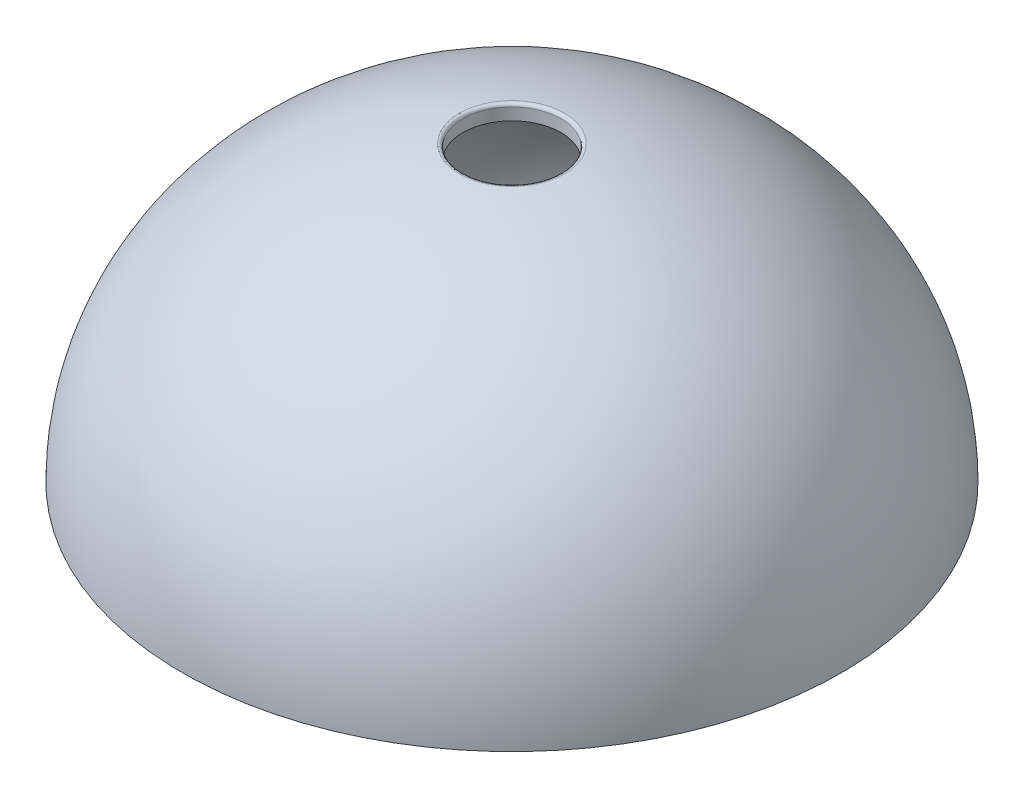
SolidWorks part; units mm, degrees
ref_plane "Front Plane" through (0, 0, 0) normal (0, 0, 1) x (1, 0, 0)
ref_plane "Top Plane" through (0, 0, 0) normal (0, 1, 0) x (1, 0, 0)
ref_plane "Right Plane" through (0, 0, 0) normal (1, 0, 0) x (0, 0, -1)
sketch "Bell Ellipse Profile" plane through (0, 0, 0) normal (0, 0, 1) x (1, 0, 0)
  line L0 (-18.7071, 0) -> (18.7071, 0) construction
  line L1 (0, -20.5619) -> (0, 20.5619) construction
  line L2 (10.75, 0) -> (0, 0)
  line L3 (0, 9.7) -> (0, 0)
  ellipse E0 centre (0, 0) end of major axis (10.75, 0) minor radius 9.7 (10.75, 0) -> (0, 9.7) ccw
  point P10 (0, 0)
  point P13 (0, 0)
revolve "Bell Hemisphere" add sketch "Bell Ellipse Profile" angle 360 about L1
ref_plane "Bell Hole Plane" through (0, 9.7, 0) normal (0, -1, 0) x (-1, 0, 0)
shell "Bell Shell" thickness 0.5
sketch "Hole Circle" plane through (0, 9.7, 0) normal (0, -1, 0) x (-1, 0, 0)
  circle A0 centre (0, 0) radius 1.6
extrude "Hole Cut" cut sketch "Hole Circle" along normal through all
fillet "Hole Fillet" radius 0.1 1 edges at (0, 9.592, -1.6)
